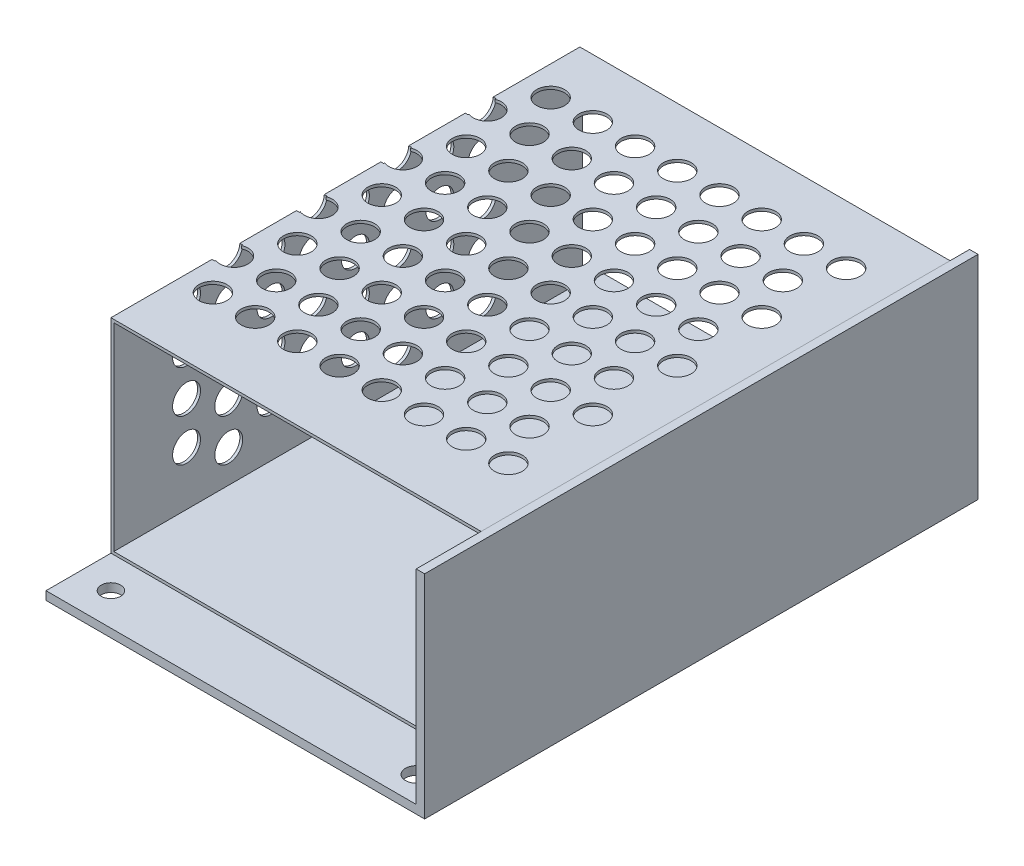
SolidWorks part; units mm, degrees
ref_plane "Front Plane" through (0, 0, 0) normal (0, 0, 1) x (1, 0, 0)
ref_plane "Top Plane" through (0, 0, 0) normal (0, 1, 0) x (1, 0, 0)
ref_plane "Right Plane" through (0, 0, 0) normal (1, 0, 0) x (0, 0, -1)
sketch "Sketch1" plane through (0, 0, 0) normal (0, 1, 0) x (1, 0, 0)
  line L1 (-29.15, -42.6) -> (29.15, -42.6)
  line L2 (-29.15, -42.6) -> (-29.15, 42.6)
  line L3 (-29.15, 42.6) -> (29.15, 42.6)
  line L4 (29.15, -42.6) -> (29.15, 42.6)
  line L5 (-29.15, -42.6) -> (29.15, 42.6) construction
  line L6 (-29.15, 42.6) -> (29.15, -42.6) construction
  point P0 (0, 0)
  dimension "D1" = 85.2
  dimension "D2" = 58.3
extrude "Boss-Extrude1" add sketch "Sketch1" along normal blind 1.3
sketch "Sketch2" plane through (0, 1.3, 0) normal (0, 1, 0) x (1, 0, 0)
  line L0 (-29.15, -42.6) -> (29.15, -42.6) construction
  line L1 (29.15, 42.6) -> (27.85, 42.6)
  line L2 (29.15, 42.6) -> (29.15, -42.6)
  line L3 (29.15, -42.6) -> (27.85, -42.6)
  line L4 (27.85, 42.6) -> (27.85, -42.6)
  dimension "D1" = 1.3
extrude "Boss-Extrude2" add sketch "Sketch2" along normal blind 31.4
sketch "Sketch3" plane through (0, 1.3, 0) normal (0, 1, 0) x (1, 0, 0)
  line L2 (-29.15, 42.6) -> (-29.15, -42.6) construction
  line L3 (-29.15, -42.6) -> (27.85, -42.6) construction
  circle A0 centre (-24.15, -37.6) radius 1.5
  circle A1 centre (-24.15, 29.4) radius 1.5
  circle A2 centre (23.85, -38.6) radius 1.65
  dimension "D1" = 5
  dimension "D2" = 5
  dimension "D3" = 3
  dimension "D5" = 67
  dimension "D6" = 3.3
  dimension "D7" = 4
  dimension "D8" = 48
  dimension "D4" = 2
extrude "Cut-Extrude1" cut sketch "Sketch3" against normal up to next
sketch "Sketch4" plane through (0, 1.3, 0) normal (0, 1, 0) x (1, 0, 0)
  line L0 (27.85, 42.6) -> (27.85, -42.6) construction
  line L1 (27.85, 39.6) -> (-29.15, 39.6)
  line L2 (27.85, 39.6) -> (27.85, -32.6)
  line L3 (27.85, -32.6) -> (-29.15, -32.6)
  line L4 (-29.15, 39.6) -> (-29.15, -32.6)
  line L5 (-29.15, 42.6) -> (-29.15, -42.6) construction
  line L6 (27.85, 42.6) -> (-29.15, 42.6) construction
  line L7 (-29.15, -42.6) -> (27.85, -42.6) construction
  dimension "D1" = 3
  dimension "D2" = 10
extrude "Boss-Extrude3" add sketch "Sketch4" along normal blind 31.4 separate body
shell "Shell1" thickness 0.44
sketch "Sketch5" plane through (0, 32.7, 0) normal (0, 1, 0) x (1, 0, 0)
  line L0 (27.85, 39.6) -> (-29.15, 39.6) construction
  line L1 (27.85, 42.6) -> (27.85, -42.6) construction
  circle A0 centre (20.85, 30.6) radius 2.15
  circle A1 centre (17.6, 24.1) radius 2.15
  circle A2 centre (14.35, 30.6) radius 2.15
  circle A3 centre (11.1, 24.1) radius 2.15
  circle A4 centre (7.85, 30.6) radius 2.15
  circle A5 centre (4.6, 24.1) radius 2.15
  circle A6 centre (1.35, 30.6) radius 2.15
  circle A7 centre (-1.9, 24.1) radius 2.15
  circle A8 centre (-5.15, 30.6) radius 2.15
  circle A9 centre (-8.4, 24.1) radius 2.15
  circle A10 centre (-11.65, 30.6) radius 2.15
  circle A11 centre (-14.9, 24.1) radius 2.15
  circle A12 centre (-18.15, 30.6) radius 2.15
  circle A13 centre (-21.4, 24.1) radius 2.15
  circle A14 centre (-24.65, 30.6) radius 2.15
  circle A15 centre (-27.9, 24.1) radius 2.15
  circle A16 centre (20.85, 17.6) radius 2.15
  circle A17 centre (17.6, 11.1) radius 2.15
  circle A18 centre (14.35, 17.6) radius 2.15
  circle A19 centre (11.1, 11.1) radius 2.15
  circle A20 centre (7.85, 17.6) radius 2.15
  circle A21 centre (4.6, 11.1) radius 2.15
  circle A22 centre (1.35, 17.6) radius 2.15
  circle A23 centre (-1.9, 11.1) radius 2.15
  circle A24 centre (-5.15, 17.6) radius 2.15
  circle A25 centre (-8.4, 11.1) radius 2.15
  circle A26 centre (-11.65, 17.6) radius 2.15
  circle A27 centre (-14.9, 11.1) radius 2.15
  circle A28 centre (-18.15, 17.6) radius 2.15
  circle A29 centre (-21.4, 11.1) radius 2.15
  circle A30 centre (-24.65, 17.6) radius 2.15
  circle A31 centre (-27.9, 11.1) radius 2.15
  circle A32 centre (20.85, 4.6) radius 2.15
  circle A33 centre (17.6, -1.9) radius 2.15
  circle A34 centre (14.35, 4.6) radius 2.15
  circle A35 centre (11.1, -1.9) radius 2.15
  circle A36 centre (7.85, 4.6) radius 2.15
  circle A37 centre (4.6, -1.9) radius 2.15
  circle A38 centre (1.35, 4.6) radius 2.15
  circle A39 centre (-1.9, -1.9) radius 2.15
  circle A40 centre (-5.15, 4.6) radius 2.15
  circle A41 centre (-8.4, -1.9) radius 2.15
  circle A42 centre (-11.65, 4.6) radius 2.15
  circle A43 centre (-14.9, -1.9) radius 2.15
  circle A44 centre (-18.15, 4.6) radius 2.15
  circle A45 centre (-21.4, -1.9) radius 2.15
  circle A46 centre (-24.65, 4.6) radius 2.15
  circle A47 centre (-27.9, -1.9) radius 2.15
  circle A48 centre (20.85, -8.4) radius 2.15
  circle A49 centre (17.6, -14.9) radius 2.15
  circle A50 centre (14.35, -8.4) radius 2.15
  circle A51 centre (11.1, -14.9) radius 2.15
  circle A52 centre (7.85, -8.4) radius 2.15
  circle A53 centre (4.6, -14.9) radius 2.15
  circle A54 centre (1.35, -8.4) radius 2.15
  circle A55 centre (-1.9, -14.9) radius 2.15
  circle A56 centre (-5.15, -8.4) radius 2.15
  circle A57 centre (-8.4, -14.9) radius 2.15
  circle A58 centre (-11.65, -8.4) radius 2.15
  circle A59 centre (-14.9, -14.9) radius 2.15
  circle A60 centre (-18.15, -8.4) radius 2.15
  circle A61 centre (-21.4, -14.9) radius 2.15
  circle A62 centre (-24.65, -8.4) radius 2.15
  circle A63 centre (-27.9, -14.9) radius 2.15
  circle A64 centre (20.85, -21.4) radius 2.15
  circle A65 centre (14.35, -21.4) radius 2.15
  circle A66 centre (7.85, -21.4) radius 2.15
  circle A67 centre (1.35, -21.4) radius 2.15
  circle A68 centre (-5.15, -21.4) radius 2.15
  circle A69 centre (-11.65, -21.4) radius 2.15
  circle A70 centre (-18.15, -21.4) radius 2.15
  circle A71 centre (-24.65, -21.4) radius 2.15
  dimension "D1" = 9
  dimension "D2" = 4.3
  dimension "D3" = 7
  dimension "D4" = 4.3
  dimension "D5" = 6.5
  dimension "D6" = 3.25
  dimension "D8" = 6.5
  dimension "D10" = 6.5
  dimension "D12" = 6.5
  dimension "D7" = 8
  dimension "D9" = 4
  dimension "D11" = 2
extrude "Cut-Extrude2" cut sketch "Sketch5" against normal up to surface (0.44 mm away) up to face at (-0.65, 32.26, -3.5)
sketch "Sketch6" plane through (-29.15, 0, 0) normal (-1, 0, 0) x (0, 0, 1)
  line L0 (-24.1, 32.7) -> (-24.1, 1.3) construction
  line L1 (-21.95, 32.7) -> (-26.25, 32.7) construction
  line L2 (-42.6, 1.3) -> (42.6, 1.3) construction
  circle A0 centre (-24.1, 6.8) radius 2.15
  circle A1 centre (-17.6, 10.05) radius 2.15
  circle A2 centre (-11.1, 6.8) radius 2.15
  circle A3 centre (-4.6, 10.05) radius 2.15
  circle A4 centre (1.9, 6.8) radius 2.15
  circle A5 centre (8.4, 10.05) radius 2.15
  circle A6 centre (14.9, 6.8) radius 2.15
  circle A7 centre (21.4, 10.05) radius 2.15
  circle A8 centre (-11.1, 13.3) radius 2.15
  circle A9 centre (-4.6, 16.55) radius 2.15
  circle A10 centre (1.9, 13.3) radius 2.15
  circle A11 centre (8.4, 16.55) radius 2.15
  circle A12 centre (14.9, 13.3) radius 2.15
  circle A13 centre (21.4, 16.55) radius 2.15
  circle A14 centre (-11.1, 19.8) radius 2.15
  circle A15 centre (-4.6, 23.05) radius 2.15
  circle A16 centre (1.9, 19.8) radius 2.15
  circle A17 centre (8.4, 23.05) radius 2.15
  circle A18 centre (14.9, 19.8) radius 2.15
  circle A19 centre (21.4, 23.05) radius 2.15
  circle A20 centre (-11.1, 26.3) radius 2.15
  circle A21 centre (-4.6, 29.55) radius 2.15
  circle A22 centre (1.9, 26.3) radius 2.15
  circle A23 centre (8.4, 29.55) radius 2.15
  circle A24 centre (14.9, 26.3) radius 2.15
  circle A25 centre (21.4, 29.55) radius 2.15
  circle A26 centre (-11.1, 32.8) radius 2.15
  circle A27 centre (-4.6, 36.05) radius 2.15
  circle A28 centre (1.9, 32.8) radius 2.15
  circle A29 centre (8.4, 36.05) radius 2.15
  circle A30 centre (14.9, 32.8) radius 2.15
  circle A31 centre (21.4, 36.05) radius 2.15
  circle A32 centre (-24.1, 13.3) radius 2.15
  circle A33 centre (-17.6, 16.55) radius 2.15
  circle A34 centre (-24.1, 19.8) radius 2.15
  circle A35 centre (-17.6, 23.05) radius 2.15
  circle A36 centre (-24.1, 26.3) radius 2.15
  circle A37 centre (-17.6, 29.55) radius 2.15
  circle A38 centre (-24.1, 32.8) radius 2.15
  circle A39 centre (-17.6, 36.05) radius 2.15
  dimension "D1" = 4.3
  dimension "D2" = 5.5
  dimension "D3" = 4.3
  dimension "D4" = 3.25
  dimension "D5" = 6.5
  dimension "D8" = 6.5
  dimension "D9" = 13
  dimension "D10" = 9.75
  dimension "D6" = 4
  dimension "D7" = 5
extrude "Cut-Extrude3" cut sketch "Sketch6" against normal up to surface (0.44 mm away) up to face at (-28.71, 27.1733, -4.2333)
